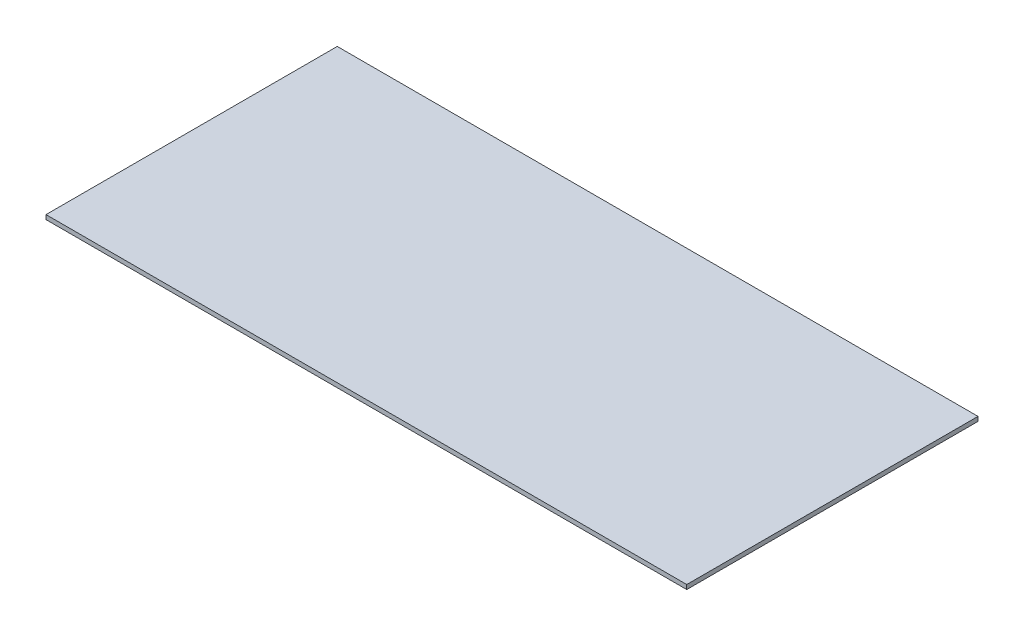
SolidWorks part; units mm, degrees
ref_plane "Plano frontal" through (0, 0, 0) normal (0, 0, 1) x (1, 0, 0)
ref_plane "Plano superior" through (0, 0, 0) normal (0, 1, 0) x (1, 0, 0)
ref_plane "Plano direito" through (0, 0, 0) normal (1, 0, 0) x (0, 0, -1)
sketch "Esboço2" plane through (0, 0, 0) normal (0, 1, 0) x (1, 0, 0)
  line L1 (16.0802, 44.4444) -> (456.0802, 44.4444)
  line L2 (16.0802, 44.4444) -> (16.0802, -155.5556)
  line L3 (16.0802, -155.5556) -> (456.0802, -155.5556)
  line L4 (456.0802, 44.4444) -> (456.0802, -155.5556)
  dimension "D1" = 200
  dimension "D2" = 440
extrude "Ressalto-extrusão3" add sketch "Esboço2" along normal blind 3 contours L2 L1 L4 L3
sketch "Esboço3" plane through (0, 0, 0) normal (0, 1, 0) x (1, 0, 0)
  line L0 (16.0802, 44.4444) -> (16.0802, -155.5556) construction
  line L1 (34.0802, -21.5556) -> (84.0802, -21.5556)
  line L2 (34.0802, -21.5556) -> (34.0802, -91.5556)
  line L3 (34.0802, -91.5556) -> (84.0802, -91.5556)
  line L4 (84.0802, -21.5556) -> (84.0802, -91.5556)
  line L5 (16.0802, -155.5556) -> (456.0802, -155.5556) construction
  point P5 (34.0802, -56.5556)
  dimension "D1" = 70
  dimension "D2" = 50
  dimension "D3" = 18
  dimension "D4" = 64
extrude "Ressalto-extrusão4" add sketch "Esboço3" against normal blind 15
